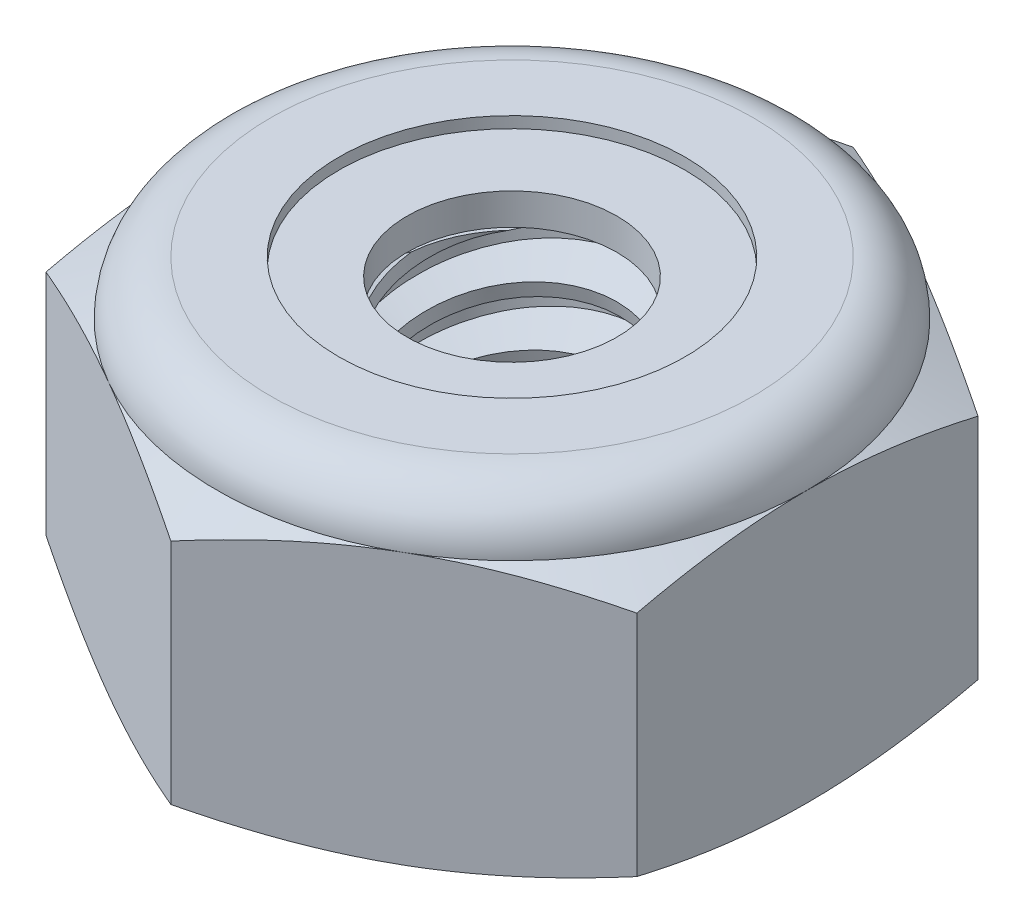
SolidWorks part; units mm, degrees
material "AISI 304"
ref_plane "Front" through (0, 0, 0) normal (0, 0, 1) x (1, 0, 0)
ref_plane "Top" through (0, 0, 0) normal (0, 1, 0) x (1, 0, 0)
ref_plane "Right" through (0, 0, 0) normal (1, 0, 0) x (0, 0, -1)
sketch "Sketch1" plane through (0, 0, 0) normal (0, 1, 0) x (1, 0, 0)
  line L1 (0, 4.5827) -> (-3.9688, 2.2914)
  line L2 (-3.9688, 2.2914) -> (-3.9688, -2.2914)
  line L3 (-3.9688, -2.2914) -> (0, -4.5827)
  line L4 (0, -4.5827) -> (3.9688, -2.2914)
  line L5 (3.9688, -2.2914) -> (3.9687, 2.2914)
  line L6 (3.9687, 2.2914) -> (0, 4.5827)
  circle A0 centre (0, 0) radius 3.9688 construction
  dimension "Hex Flats" = 7.9375
extrude "Extrude1" add sketch "Sketch1" along normal blind 4.3656
sketch "Sketch2" plane through (0, 0, 0) normal (1, 0, 0) x (0, 0, -1)
  line L0 (-1.7526, 0) -> (-1.7526, 4.3656) construction
  line L1 (0, 0) -> (1.7526, 0)
  line L2 (0, 0) -> (0, 4.3656)
  line L3 (0, 4.3656) -> (1.7526, 4.3656)
  line L4 (1.7526, 0) -> (1.7526, 4.3656)
  line L5 (-2.2914, 4.3656) -> (2.2914, 4.3656) construction
  line L7 (0, -1.7526) -> (0, 0) construction
  dimension "Thread Dia" = 3.5052
revolve "Revolve1" add sketch "Sketch2" angle 360 about L7
sketch "Sketch3" plane through (0, 0, 0) normal (1, 0, 0) x (0, 0, -1)
  line L0 (1.7526, 4.3656) -> (-1.7526, 4.3656) construction
  line L1 (-1.7526, 4.3656) -> (-1.7526, 3.5719) construction
  line L2 (-1.7526, 3.5719) -> (1.7526, 4.3656) construction
  line L3 (1.7526, 4.3656) -> (1.7745, 4.2689) construction
  line L4 (1.7745, 4.2689) -> (1.9279, 3.5915)
  line L5 (1.9279, 3.5915) -> (1.4541, 3.7385)
  line L6 (1.4541, 3.7385) -> (1.4103, 3.932)
  line L7 (1.4103, 3.932) -> (1.7745, 4.2689)
  line L8 (1.4322, 3.8353) -> (1.8512, 3.9302) construction
  line L9 (1.7526, 4.3656) -> (1.7526, 3.9078) construction
  line L10 (1.7526, 3.9078) -> (-1.7526, 3.1141) construction
  line L11 (-1.7526, 3.1141) -> (-1.7526, 3.5719) construction
  line L12 (-0.1935, 4.3656) -> (0.1935, 2.6563) construction
  line L13 (-1.7526, 0) -> (-1.7526, 4.3656) construction
  line L14 (0, 4.3656) -> (1.7526, 4.3656) construction
  line L15 (1.7526, 0) -> (1.7526, 4.3656) construction
  point P13 (0, 3.511)
  dimension "D1" = 0.0992
  dimension "D2" = 0.1984
  dimension "Thread Pitch" = 0.7937
  dimension "D4" = 60
  dimension "D5" = 0.7937
revolve "Cut-Revolve1" cut sketch "Sketch3" angle 360 about L12
pattern_linear "LPattern1" count 6 spacing 0.7937 along (0, -1, 0) count 2 spacing 0.7937 along (0, 1, 0) of "Cut-Revolve1"
sketch "Sketch4" plane through (0, 0, 0) normal (1, 0, 0) x (0, 0, -1)
  line L0 (0, 4.3656) -> (1.7526, 4.3656)
  line L1 (1.7526, 4.3656) -> (1.4103, 4.206)
  line L2 (1.4103, 4.206) -> (1.4103, 0.1596)
  line L3 (1.4103, 0.1596) -> (1.7526, 0)
  line L4 (1.7526, 0) -> (0, 0)
  line L5 (0, 0) -> (0, 4.3656)
  line L6 (1.7526, 0) -> (1.7526, 4.3656) construction
  line L7 (0, 4.3656) -> (1.7526, 4.3656) construction
  line L8 (0, 0) -> (1.7526, 0) construction
  line L9 (0, 0) -> (0, 4.3656) construction
  line L10 (0, 4.3656) -> (0, 4.7433) construction
  dimension "D1" = 25
revolve "Cut-Revolve2" cut sketch "Sketch4" angle 360 about L10
combine bodies "Combine1" operation type subtract main body 112 bodies to subtract 111
sketch "Sketch5" plane through (0, 0, 0) normal (1, 0, 0) x (0, 0, -1)
  line L0 (0, 0) -> (3.9688, 0)
  line L1 (3.9688, 0) -> (4.5827, 0.2863)
  line L2 (4.5827, 0.2863) -> (4.5827, 3.3517)
  line L3 (4.5827, 3.3517) -> (3.9688, 3.638)
  line L4 (3.2411, 4.3656) -> (3.2411, 5.6356)
  line L5 (3.2411, 5.6356) -> (5.8527, 5.6356)
  line L6 (5.8527, 5.6356) -> (5.8527, -1.27)
  line L7 (5.8527, -1.27) -> (0, -1.27)
  line L8 (0, -1.27) -> (0, 0)
  line L9 (3.9688, 3.638) -> (3.9688, 0) construction
  line L10 (0, 0) -> (1.7526, 0) construction
  line L13 (4.5827, 1.819) -> (5.8527, 1.819) construction
  line L14 (4.5827, 4.3656) -> (4.5827, 0) construction
  line L15 (0, 0) -> (0, 5.6356) construction
  line L20 (0, 5.6356) -> (3.2411, 5.6356) construction
  line L22 (0, 4.3656) -> (1.7526, 4.3656) construction
  arc A0 (3.9688, 3.638) -> (3.2411, 4.3656) centre (3.2411, 3.638) ccw
  dimension "D1" = 25
  dimension "D2" = 1.27
  dimension "D3" = 4.3656
  dimension "D4" = 0.7276
revolve "Cut-Revolve3" cut sketch "Sketch5" angle 360 about L15
sketch "Sketch6" plane through (0, 0, 0) normal (1, 0, 0) x (0, 0, -1)
  line L0 (0, 3.638) -> (3.8164, 3.638)
  line L1 (3.2411, 4.2132) -> (2.3257, 4.2132)
  line L2 (0, 5.6356) -> (0, 3.638)
  line L3 (2.3257, 5.6356) -> (0, 5.6356)
  line L4 (0, 5.6356) -> (3.2411, 5.6356) construction
  line L5 (0, 0) -> (0, 5.6356) construction
  line L6 (0, 5.6356) -> (0, 44.323) construction
  line L7 (2.3257, 4.2132) -> (2.3257, 5.6356)
  line L8 (3.2411, 4.3656) -> (3.2411, 4.2132) construction
  line L9 (2.3257, 4.2132) -> (1.4103, 4.2132) construction
  line L10 (1.4103, 4.2132) -> (1.4103, 4.206) construction
  arc A0 (3.8164, 3.638) -> (3.2411, 4.2132) centre (3.2411, 3.638) ccw
  arc A1 (3.9688, 3.638) -> (3.2411, 4.3656) centre (3.2411, 3.638) ccw construction
  dimension "D1" = 0.1524
revolve "Cut-Revolve4" cut sketch "Sketch6" angle 360 about L6
sketch "Sketch7" plane through (0, 0, 0) normal (1, 0, 0) x (0, 0, -1)
  line L0 (1.4103, 3.7142) -> (3.7343, 3.7142)
  line L1 (3.2411, 4.137) -> (1.4103, 4.137)
  line L2 (1.4103, 4.137) -> (1.4103, 3.7142)
  line L3 (1.4103, 3.7142) -> (0, 3.7142) construction
  line L4 (0, 3.7142) -> (0, 4.137) construction
  line L5 (0, 4.137) -> (1.4103, 4.137) construction
  line L6 (1.4103, 3.7142) -> (1.4103, 3.638) construction
  line L7 (0, 3.638) -> (3.8164, 3.638) construction
  line L8 (3.2411, 4.137) -> (3.2411, 4.2132) construction
  arc A0 (3.7343, 3.7142) -> (3.2411, 4.137) centre (3.2411, 3.638) ccw
  arc A2 (3.8164, 3.638) -> (3.2411, 4.2132) centre (3.2411, 3.638) ccw construction
  dimension "D1" = 0.0762
revolve "Revolve2" add sketch "Sketch7" angle 360 about L4
equation "\"D1@Sketch3\"=\"Thread Pitch@Sketch3\"/8"
equation "\"D2@Sketch3\"=\"Thread Pitch@Sketch3\"/4"
equation "\"D5@Sketch3\"=\"Thread Pitch@Sketch3\""
equation "\"D4@LPattern1\"=\"Thread Pitch@Sketch3\""
equation "\"D3@LPattern1\"=\"Thread Pitch@Sketch3\""
equation "\"D1@LPattern1\"=\"Height@Extrude1\"/\"Thread Pitch@Sketch3\""
equation "\"D4@Sketch5\"=\"Height@Extrude1\"/6"
